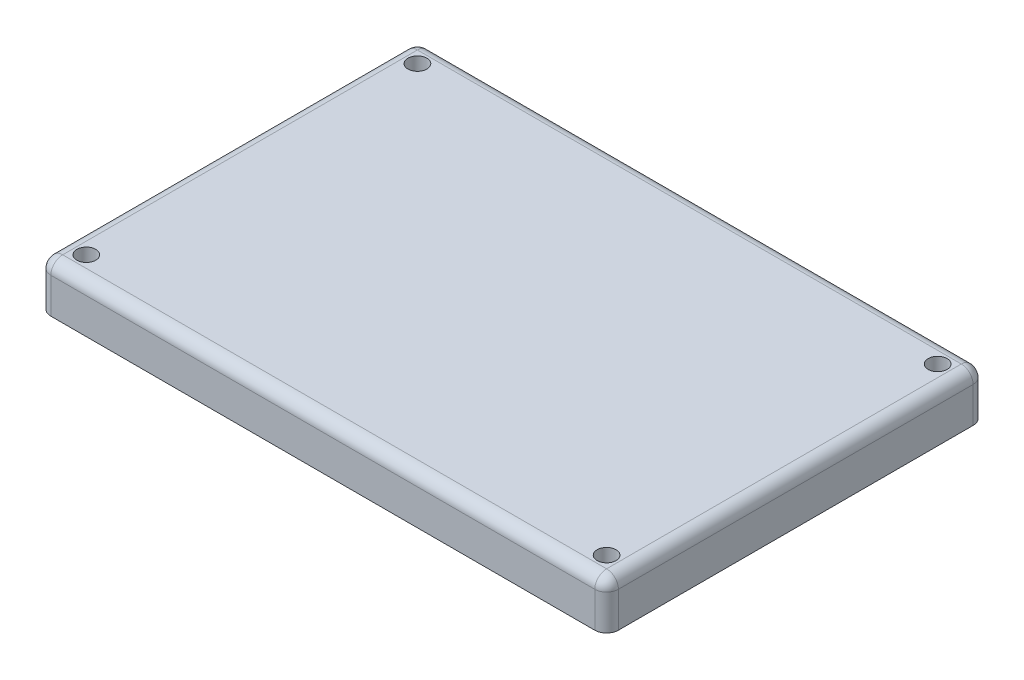
SolidWorks part; units mm, degrees
material "Acrylic (Medium-high impact)"
ref_plane "Front Plane" through (0, 0, 0) normal (0, 0, 1) x (1, 0, 0)
ref_plane "Top Plane" through (0, 0, 0) normal (0, 1, 0) x (1, 0, 0)
ref_plane "Right Plane" through (0, 0, 0) normal (1, 0, 0) x (0, 0, -1)
sketch "Sketch1" plane through (0, 0, 0) normal (0, 1, 0) x (1, 0, 0)
  line L0 (0, 0) -> (60.96, 0)
  line L1 (60.96, 0) -> (60.96, 40.64)
  line L2 (60.96, 40.64) -> (0, 40.64)
  line L3 (0, 40.64) -> (0, 0)
extrude "Boss-Extrude1" add sketch "Sketch1" along normal blind 5.08
shell "Shell1" thickness 2.54
sketch "Sketch2" plane through (0, 0, 0) normal (0, -1, 0) x (1, 0, 0)
  circle A0 centre (58.42, -38.1) radius 2.54
  circle A1 centre (58.42, -2.54) radius 2.54
  circle A2 centre (2.54, -2.54) radius 2.54
  circle A3 centre (2.54, -38.1) radius 2.54
extrude "Boss-Extrude2" add sketch "Sketch2" against normal blind 5.08
sketch "Sketch3" plane through (0, 0, 0) normal (0, -1, 0) x (1, 0, 0)
  line L0 (58.42, -35.56) -> (58.42, -38.1) construction
  line L1 (5.08, -38.1) -> (2.54, -38.1) construction
  line L2 (2.54, -5.08) -> (2.54, -2.54) construction
  line L3 (58.42, -5.08) -> (58.42, -2.54) construction
  circle A0 centre (58.42, -38.1) radius 1.016
  circle A1 centre (58.42, -2.54) radius 1.016
  circle A2 centre (2.54, -2.54) radius 1.016
  circle A3 centre (2.54, -38.1) radius 1.016
extrude "Cut-Extrude1" cut sketch "Sketch3" against normal blind 5.08
fillet "Fillet2" radius 1.27 8 edges at (60.96, 2.54, -40.64) (60.96, 5.08, -20.32) (60.96, 2.54, 0) (30.48, 5.08, 0) (0, 2.54, 0) (0, 2.54, -40.64) (30.48, 5.08, -40.64) (0, 5.08, -20.32)
